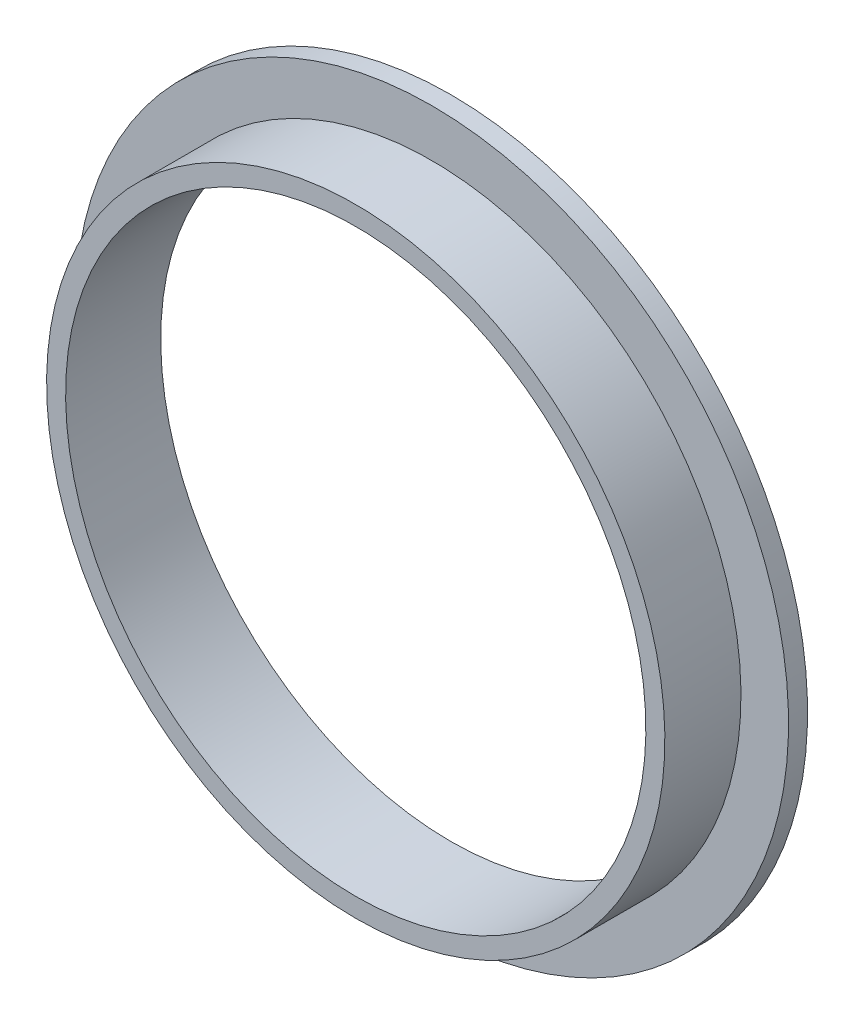
SolidWorks part; units mm, degrees
ref_plane "Front Plane" through (0, 0, 0) normal (0, 0, 1) x (1, 0, 0)
ref_plane "Top Plane" through (0, 0, 0) normal (0, 1, 0) x (1, 0, 0)
ref_plane "Right Plane" through (0, 0, 0) normal (1, 0, 0) x (0, 0, -1)
sketch "Sketch1" plane through (0, 0, 0) normal (1, 0, 0) x (0, 0, -1)
  line L0 (-7.9375, 0) -> (7.9375, 0) construction
  line L1 (-7.9375, 48.4188) -> (7.9375, 48.4188)
  line L2 (7.9375, 48.4188) -> (7.9375, 59.5312)
  line L3 (7.9375, 59.5312) -> (4.7625, 59.5312)
  line L4 (4.7625, 59.5312) -> (4.7625, 51.5938)
  line L5 (4.7625, 51.5938) -> (-7.9375, 51.5938)
  line L6 (-7.9375, 51.5938) -> (-7.9375, 48.4188)
  point P2 (0, 0)
  dimension "D1" = 15.875
  dimension "D2" = 51.5938
  dimension "D3" = 3.175
  dimension "D4" = 3.175
  dimension "D5" = 11.1125
revolve "Revolve1" add sketch "Sketch1" angle 360 about L0
